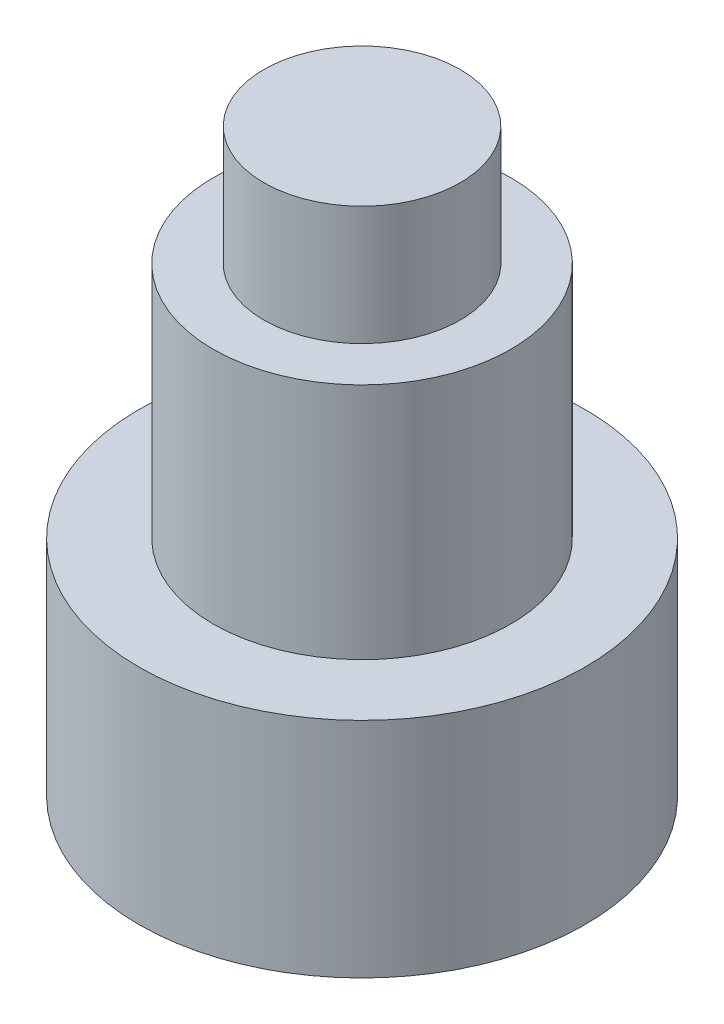
SolidWorks part; units mm, degrees
ref_plane "Front Plane" through (0, 0, 0) normal (0, 0, 1) x (1, 0, 0)
ref_plane "Top Plane" through (0, 0, 0) normal (0, 1, 0) x (1, 0, 0)
ref_plane "Right Plane" through (0, 0, 0) normal (1, 0, 0) x (0, 0, -1)
sketch "Sketch1" plane through (0, 0, 0) normal (0, 1, 0) x (1, 0, 0)
  circle A0 centre (0, 0) radius 3.75
extrude "Boss-Extrude1" add sketch "Sketch1" along normal blind 7.75
sketch "Sketch2" plane through (0, 7.75, 0) normal (0, 1, 0) x (1, 0, 0)
  circle A0 centre (0, 0) radius 2.5
  circle A1 centre (0, 0) radius 3.75
extrude "Cut-Extrude1" cut sketch "Sketch2" against normal blind 4
sketch "Sketch3" plane through (0, 7.75, 0) normal (0, 1, 0) x (1, 0, 0)
  circle A0 centre (0, 0) radius 1.65
extrude "Boss-Extrude2" add sketch "Sketch3" along normal blind 2
